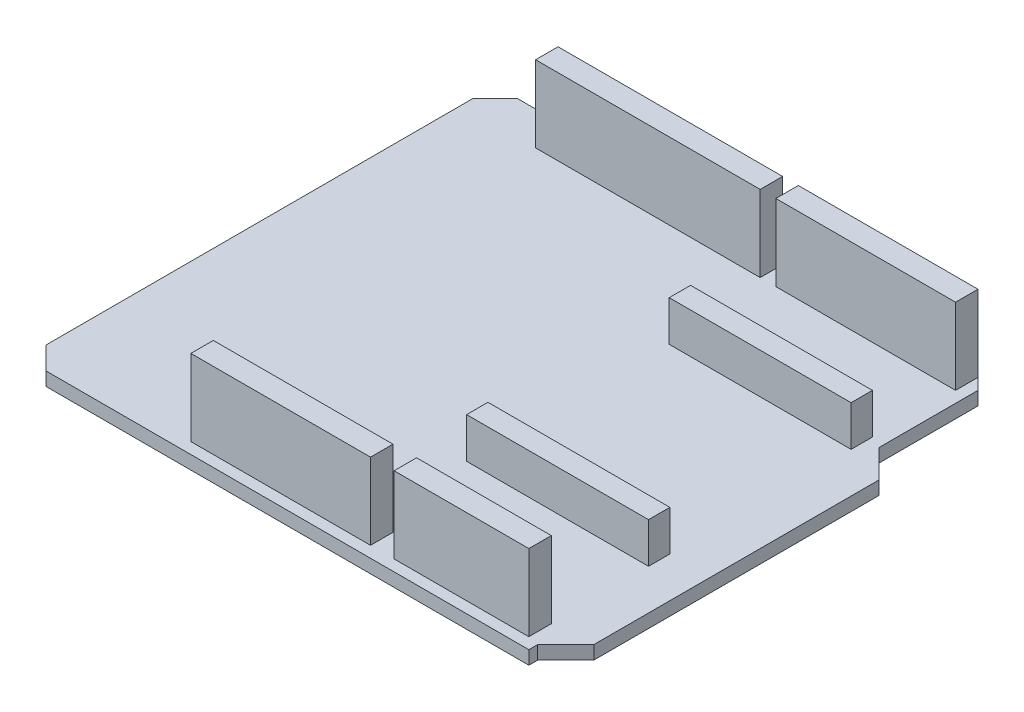
SolidWorks part; units mm, degrees
ref_plane "Front Plane" through (0, 0, 0) normal (0, 0, 1) x (1, 0, 0)
ref_plane "Top Plane" through (0, 0, 0) normal (0, 1, 0) x (1, 0, 0)
ref_plane "Right Plane" through (0, 0, 0) normal (1, 0, 0) x (0, 0, -1)
sketch "Sketch1" plane through (0, 0, 0) normal (0, 1, 0) x (1, 0, 0)
  line L0 (57.15, 39.608) -> (60.325, 36.433)
  line L1 (2.54, 0) -> (57.15, 0)
  line L2 (0, 2.54) -> (0, 50.8)
  line L3 (2.54, 53.34) -> (54.61, 53.34)
  line L4 (57.15, 0) -> (57.15, 1)
  line L5 (60.325, 36.433) -> (60.325, 4.175)
  line L6 (60.325, 4.175) -> (57.15, 1)
  line L7 (57.15, 39.608) -> (57.15, 50.8)
  line L8 (54.61, 53.34) -> (57.15, 50.8)
  line L9 (0, 50.8) -> (2.54, 53.34)
  line L10 (0, 2.54) -> (2.54, 0)
  point P0 (0, 0)
  point P1 (57.15, 53.34)
  point P2 (0, 53.34)
  point P7 (101.6, 38.56)
  dimension "D1" = 57.15
  dimension "D2" = 53.34
  dimension "D3" = 60.325
  dimension "D4" = 38.608
  dimension "D5" = 1
extrude "Boss-Extrude1" add sketch "Sketch1" along normal mid plane 1.524
hole_wizard "Ø1.3 (1.3) Diameter Hole1" positions "Sketch2" profile "Sketch3" hole size "Ø1.3" standard "ANSI Metric" end condition up to next
sketch "Sketch2" plane through (0, 0.762, 0) normal (0, 1, 0) x (1, 0, 0)
  line L0 (0, 50.8) -> (0, 2.54) construction
  line L1 (2.54, 0) -> (57.15, 0) construction
  line L2 (18.923, 0) -> (18.923, 2.54) construction
  line L5 (9.652, 50.8) -> (9.652, 53.34) construction
  line L6 (54.61, 53.34) -> (2.54, 53.34) construction
  line L9 (9.652, 50.8) -> (12.192, 50.8) construction
  line L10 (41.91, 2.54) -> (44.45, 2.54) construction
  line L11 (36.83, 50.8) -> (39.37, 50.8) construction
  point P0 (18.923, 2.54)
  point P2 (9.652, 50.8)
  point P25 (21.463, 2.54)
  point P26 (24.003, 2.54)
  point P27 (26.543, 2.54)
  point P28 (29.083, 2.54)
  point P29 (31.623, 2.54)
  point P30 (34.163, 2.54)
  point P31 (36.703, 2.54)
  point P36 (12.192, 50.8)
  point P37 (14.732, 50.8)
  point P38 (17.272, 50.8)
  point P39 (19.812, 50.8)
  point P40 (22.352, 50.8)
  point P41 (24.892, 50.8)
  point P42 (27.432, 50.8)
  point P43 (29.972, 50.8)
  point P44 (32.512, 50.8)
  point P47 (41.91, 2.54)
  point P49 (36.83, 50.8)
  point P56 (44.45, 2.54)
  point P57 (46.99, 2.54)
  point P58 (49.53, 2.54)
  point P59 (52.07, 2.54)
  point P60 (54.61, 2.54)
  point P71 (39.37, 50.8)
  point P72 (41.91, 50.8)
  point P73 (44.45, 50.8)
  point P74 (46.99, 50.8)
  point P75 (49.53, 50.8)
  point P76 (52.07, 50.8)
  point P77 (54.61, 50.8)
  point P194 (91.567, 2.54) [skipped]
  point P196 (89.027, 2.54) [skipped]
  point P198 (86.487, 2.54) [skipped]
  point P200 (83.947, 2.54) [skipped]
  point P202 (81.407, 2.54) [skipped]
  point P204 (78.867, 2.54) [skipped]
  point P205 (76.327, 2.54) [skipped]
  dimension "D1" = 9.652
  dimension "D2" = 50.8
  dimension "D3" = 18.923
  dimension "D5" = 2.54
  dimension "D7" = 2.54
  dimension "D8" = 41.91
  dimension "D10" = 2.54
  dimension "D11" = 36.83
  dimension "D12" = 8
  dimension "D13" = 2.54
  dimension "D4" = 8
  dimension "D6" = 10
  dimension "D9" = 6
sketch "Sketch3" plane through (18.923, 0.762, -2.54) normal (1, 0, 0) x (0, 0, 1)
  line L0 (0, 0) -> (0, 1.524)
  line L1 (0, 1.524) -> (0.65, 1.524)
  line L2 (0.65, 1.524) -> (0.65, 0)
  line L5 (0.65, 0) -> (0, 0)
  line L11 (0, -6.35) -> (0, 107.95) construction
  dimension "Thru Hole Dia." = 1.3
  dimension "Thru Hole Depth" = 1.524
sketch "Sketch6" plane through (0, 0.762, 0) normal (0, 1, 0) x (1, 0, 0)
  line L1 (8.382, 52.07) -> (33.782, 52.07)
  line L2 (8.382, 52.07) -> (8.382, 49.53)
  line L3 (8.382, 49.53) -> (33.782, 49.53)
  line L4 (33.782, 52.07) -> (33.782, 49.53)
  line L5 (35.56, 52.07) -> (55.88, 52.07)
  line L6 (35.56, 52.07) -> (35.56, 49.53)
  line L7 (35.56, 49.53) -> (55.88, 49.53)
  line L8 (55.88, 52.07) -> (55.88, 49.53)
  line L21 (17.653, 3.81) -> (37.973, 3.81)
  line L22 (17.653, 3.81) -> (17.653, 1.27)
  line L23 (17.653, 1.27) -> (37.973, 1.27)
  line L24 (37.973, 3.81) -> (37.973, 1.27)
  line L25 (40.64, 3.81) -> (55.88, 3.81)
  line L26 (40.64, 3.81) -> (40.64, 1.27)
  line L27 (40.64, 1.27) -> (55.88, 1.27)
  line L28 (55.88, 3.81) -> (55.88, 1.27)
  line L33 (32.512, 50.8) -> (33.782, 50.8) construction
  line L34 (9.652, 50.8) -> (8.382, 50.8) construction
  line L35 (36.83, 50.8) -> (35.56, 50.8) construction
  line L36 (54.61, 50.8) -> (55.88, 50.8) construction
  line L42 (18.923, 2.54) -> (17.653, 2.54) construction
  line L43 (36.703, 2.54) -> (37.973, 2.54) construction
  line L44 (40.64, 2.54) -> (41.91, 2.54) construction
  line L45 (54.61, 2.54) -> (55.88, 2.54) construction
  circle A1 centre (54.61, 2.54) radius 0.65 construction
  point P30 (9.652, 50.8)
  point P34 (18.923, 2.54)
  point P43 (54.61, 50.8)
  point P45 (36.83, 50.8)
  point P47 (32.512, 50.8)
  point P67 (0, 0)
  point P69 (41.91, 2.54)
  point P71 (36.703, 2.54)
  point P84 (0, 0)
  point P85 (0, 0)
  point P86 (0, 0)
  dimension "D1" = 2.54
  dimension "D2" = 1.27
extrude "Boss-Extrude2" add sketch "Sketch6" along normal blind 8.636 separate body
sketch "Sketch7" plane through (0, 0.762, 0) normal (0, 1, 0) x (1, 0, 0)
  line L0 (35.56, 49.53) -> (55.88, 49.53) construction
  line L1 (35.179, 40.259) -> (55.753, 40.259)
  line L2 (35.179, 40.259) -> (35.179, 37.846)
  line L3 (35.179, 37.846) -> (55.753, 37.846)
  line L4 (55.753, 40.259) -> (55.753, 37.846)
  line L5 (35.179, 14.933) -> (55.753, 14.933)
  line L6 (35.179, 14.933) -> (35.179, 17.346)
  line L7 (35.179, 17.346) -> (55.753, 17.346)
  line L8 (55.753, 14.933) -> (55.753, 17.346)
  line L9 (0, 50.8) -> (0, 2.54) construction
  dimension "D1" = 2.413
  dimension "D2" = 9.271
  dimension "D3" = 20.5
  dimension "D4" = 20.574
  dimension "D5" = 35.179
extrude "Boss-Extrude3" add sketch "Sketch7" along normal blind 4.572 separate body
